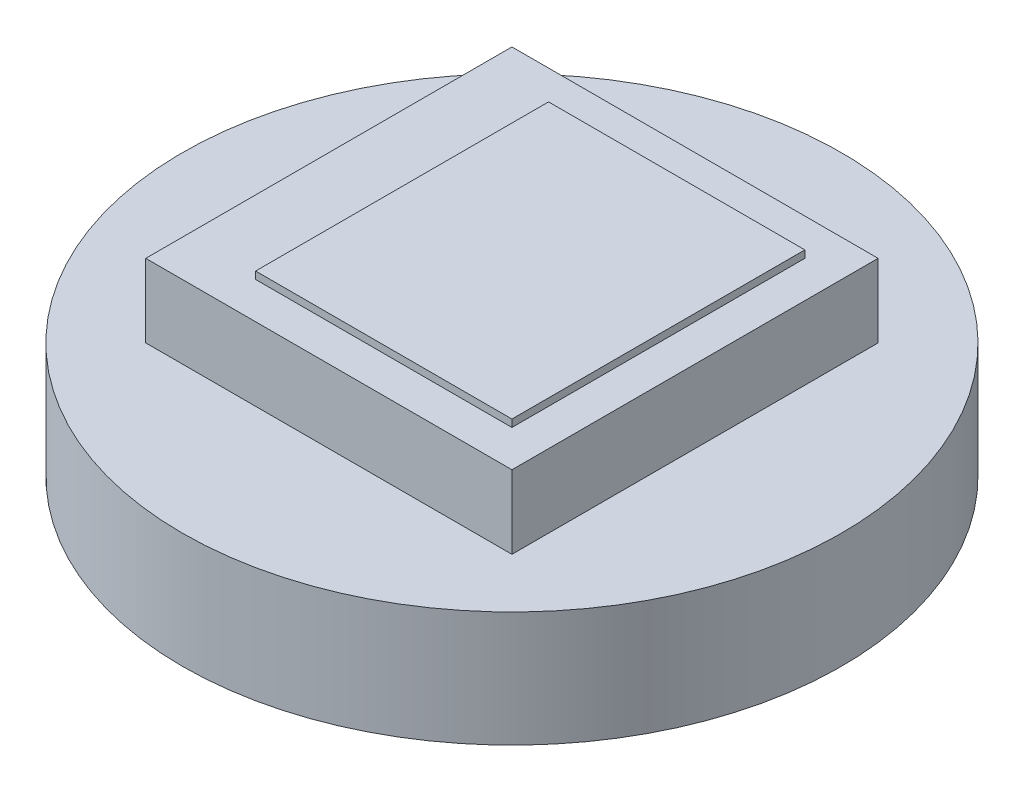
SolidWorks part; units mm, degrees
material "Custom Plastic"
ref_plane "Front Plane" through (0, 0, 0) normal (0, 0, 1) x (1, 0, 0)
ref_plane "Top Plane" through (0, 0, 0) normal (0, 1, 0) x (1, 0, 0)
ref_plane "Right Plane" through (0, 0, 0) normal (1, 0, 0) x (0, 0, -1)
sketch "Sketch1" plane through (0, 0, 0) normal (0, 1, 0) x (1, 0, 0)
  circle A0 centre (0, 0) radius 4.5
  dimension "D1" = 9
extrude "Boss-Extrude1" add sketch "Sketch1" along normal blind 1.5748
sketch "Sketch2" plane through (0, 1.5748, 0) normal (0, 1, 0) x (1, 0, 0)
  line L0 (0, 2.5) -> (0, -2.5) construction
  line L1 (-2.5, 2.5) -> (2.5, 2.5)
  line L2 (-2.5, 2.5) -> (-2.5, -2.5)
  line L3 (-2.5, -2.5) -> (2.5, -2.5)
  line L4 (2.5, 2.5) -> (2.5, -2.5)
  dimension "D1" = 5
  dimension "D2" = 5
extrude "Boss-Extrude2" add sketch "Sketch2" along normal blind 1
sketch "Sketch3" plane through (0, 2.5748, 0) normal (0, 1, 0) x (1, 0, 0)
  line L0 (0, 2) -> (0, -2) construction
  line L1 (-1.5, 2) -> (2, 2)
  line L2 (-1.5, 2) -> (-1.5, -2)
  line L3 (-1.5, -2) -> (2, -2)
  line L4 (2, 2) -> (2, -2)
  dimension "D1" = 3.5
  dimension "D2" = 4
  dimension "D3" = 2
extrude "Boss-Extrude3" add sketch "Sketch3" along normal blind 0.1
